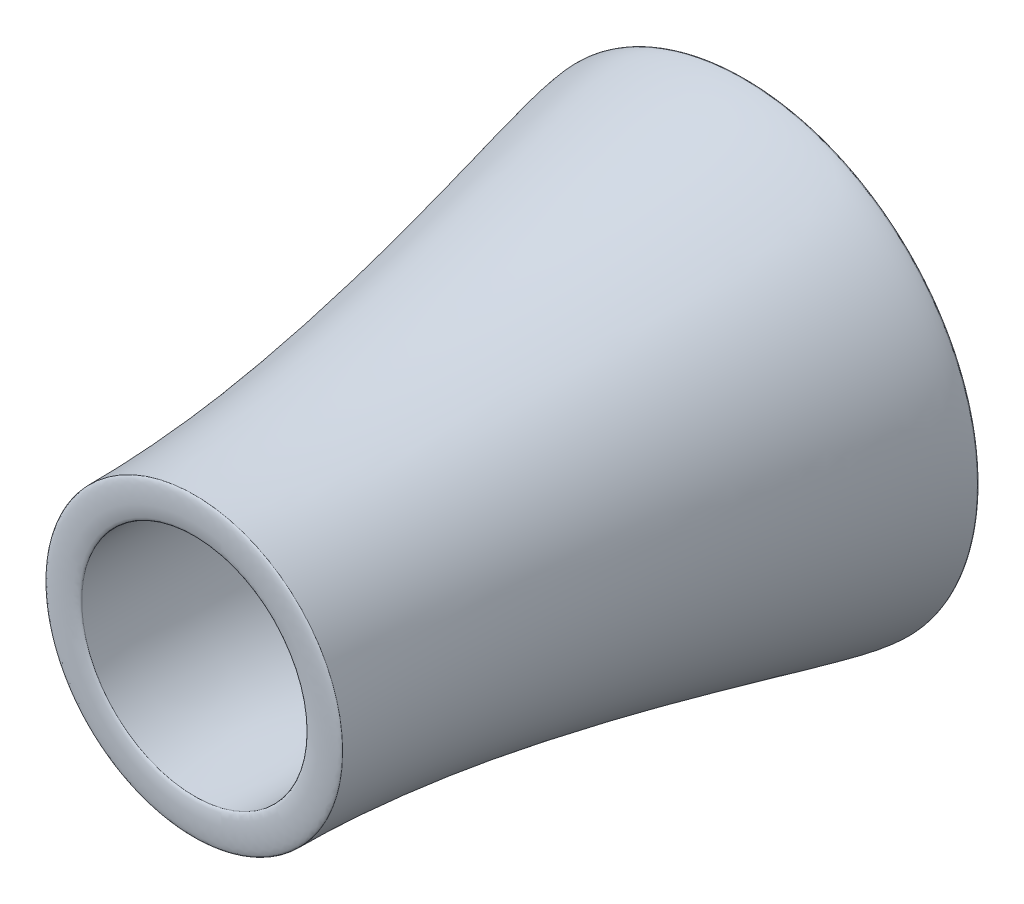
SolidWorks part; units mm, degrees
ref_plane "Front Plane" through (0, 0, 0) normal (0, 0, 1) x (1, 0, 0)
ref_plane "Top Plane" through (0, 0, 0) normal (0, 1, 0) x (1, 0, 0)
ref_plane "Right Plane" through (0, 0, 0) normal (1, 0, 0) x (0, 0, -1)
sketch "Sketch1" plane through (0, 0, 0) normal (0, 0, 1) x (1, 0, 0)
  circle A0 centre (0, 0) radius 50.8
  dimension "D1" = 101.6
ref_plane "Plane1" through (0, -254, 0) normal (0, 1, 0) x (1, 0, 0)
sketch "Sketch6" plane through (0, 0, 0) normal (0, 1, 0) x (1, 0, 0)
  line L0 (0, -99.6848) -> (0, 145.6048) construction
ref_plane "Plane2" through (0, -114.3, 0) normal (0, 1, 0) x (1, 0, 0)
sketch "Sketch12" plane through (0, 0, 0) normal (0, 1, 0) x (1, 0, 0)
  line L0 (0, -1104.7568) -> (0, -908.6135) construction
ref_plane "Plane3" through (0, 0, 203.2) normal (0, 0, 1) x (1, 0, 0)
ref_plane "Plane4" through (0, 0, 889) normal (0, 0, 1) x (1, 0, 0)
sketch "Sketch17" plane through (0, 0, 0) normal (0, 1, 0) x (1, 0, 0)
  line L0 (-259.4955, -43.5301) -> (-259.4955, 70.1436) construction
  line L1 (-110.6437, -1316.1124) -> (-110.6437, -853.5386) construction
  line L2 (-259.4955, 45.4622) -> (-387.328, 45.4622)
  line L3 (-387.328, 45.4622) -> (-387.328, -1084.8928)
  line L4 (-387.328, -1084.8928) -> (-110.6437, -1084.8928)
  spline S0 degree 3 poles (-259.4955, 45.4622) (-259.4955, -7.1736) (-207.7477, -105.8122) (-173.3147, -383.1384) (-92.4228, -818.9689) (-110.6437, -795.7842) (-110.6437, -1084.8928) knots 0 0 0 0 0.158009 0.206507 0.484977 1 1 1 1
sketch "Sketch21" plane through (0, 0, 0) normal (0, 1, 0) x (1, 0, 0)
  line L0 (-711.6099, -22.8536) -> (-711.6099, 113.778) construction
  line L1 (-450.1433, -1315.9117) -> (-450.1433, -853.874) construction
  line L2 (-603.4631, 570.8085) -> (-711.6099, 570.8085) construction
  line L3 (-342.8305, -1095.4625) -> (-450.1433, -1095.4625) construction
  line L4 (-342.8305, -1095.4625) -> (-450.1433, -1095.4625)
  line L6 (-603.4631, 570.8085) -> (-711.6099, 570.8085)
  spline S0 degree 3 poles (-603.4631, 570.8085) (-603.4631, 518.1727) (-505.6641, 359.3712) (-484.1606, 99.1872) (-304.6581, -485.2735) (-342.8305, -806.3539) (-342.8305, -1095.4625) knots 0 0 0 0 0.158009 0.206507 0.484977 1 1 1 1
  spline S1 degree 3 poles (-711.6099, 570.8085) (-711.6099, 445.4245) (-450.1433, -365.1534) (-450.1433, -1095.4625) knots 0 0 0 0 1 1 1 1
  point P10 (-711.6099, 542.8328)
  point P11 (-603.4631, 570.8085)
  point P12 (-406.9105, 170.0784)
  point P13 (-203.2063, -409.011)
  point P14 (-499.6851, 272.997)
  point P15 (-342.8305, -1104.9442)
  point P16 (-450.1433, -1095.4625)
  point P17 (-380.6239, -292.7809)
revolve "Revolve2" add sketch "Sketch21" angle 360 about L0
sketch "Sketch22" plane through (0, 0, 0) normal (0, 1, 0) x (1, 0, 0)
  line L0 (-711.6099, 570.8085) -> (-603.4631, 570.8085)
  line L1 (-603.4631, 566.9994) -> (-603.4631, 574.6176) construction
  line L2 (-711.6099, 572.2012) -> (-711.6099, 569.4158) construction
  spline S0 degree 3 poles (-711.6099, 570.8085) (-711.6099, 587.7418) (-603.4631, 587.7418) (-603.4631, 570.8085) knots 0 0 0 0 1 1 1 1
revolve "Revolve3" add sketch "Sketch22" angle 360 about L0
sketch "Sketch23" plane through (0, 0, 0) normal (0, 1, 0) x (1, 0, 0)
  line L0 (-450.1433, -1095.4625) -> (-342.8305, -1095.4625)
  line L1 (-450.1433, -1104.6736) -> (-450.1433, -1086.2514) construction
  line L2 (-342.8305, -1084.8895) -> (-342.8305, -1106.0355) construction
  spline S0 degree 3 poles (-450.1433, -1095.4625) (-450.1433, -1108.1625) (-342.8305, -1108.1625) (-342.8305, -1095.4625) knots 0 0 0 0 1 1 1 1
revolve "Revolve4" add sketch "Sketch23" angle 360 about L0
ref_plane "Plane5" through (289.9098, 0, 0) normal (1, 0, 0) x (0, 0, -1)
sketch "Sketch24" plane through (289.9098, 0, 0) normal (1, 0, 0) x (0, 0, -1)
  line L0 (-1123.5724, -17.6357) -> (119.2276, -17.6357) construction
  line L1 (-1095.4625, 0) -> (570.8085, 0) construction
  line L2 (-1095.4625, -450.1433) -> (-1095.4625, 450.1433) construction
  line L3 (570.8085, 711.6099) -> (570.8085, -711.6099) construction
  text T0 "MD-130 Gas Turbine Engine" font "TI-Nspire" height in points 160
